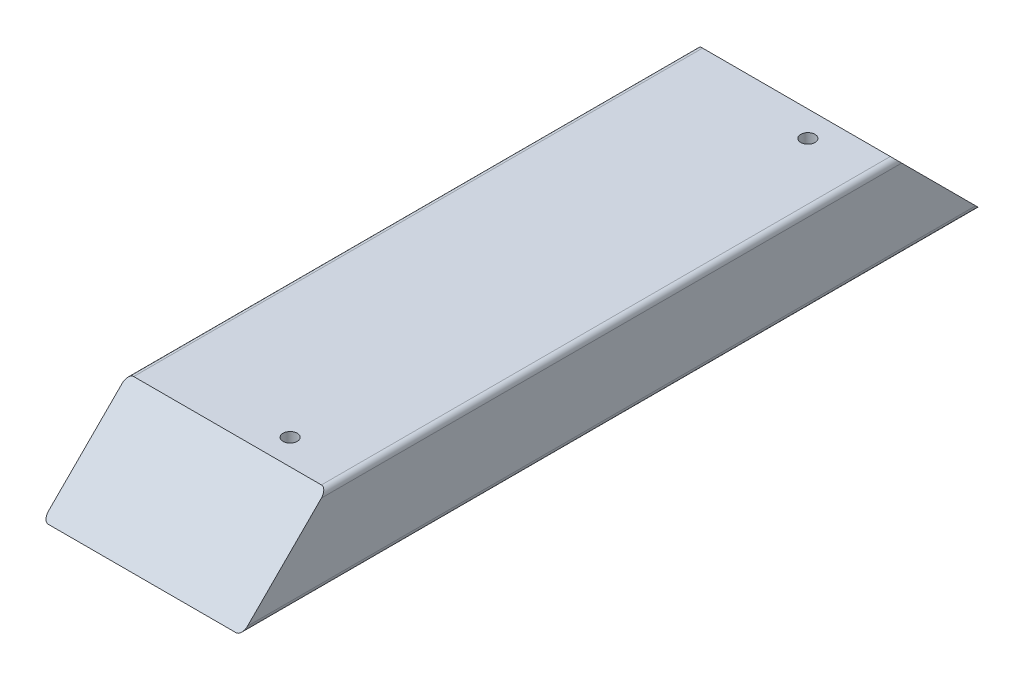
SolidWorks part; units mm, degrees
ref_plane "Front Plane" through (0, 0, 0) normal (0, 0, 1) x (1, 0, 0)
ref_plane "Top Plane" through (0, 0, 0) normal (0, 1, 0) x (1, 0, 0)
ref_plane "Right Plane" through (0, 0, 0) normal (1, 0, 0) x (0, 0, -1)
sketch "Sketch1" plane through (0, 0, 0) normal (0, 0, 1) x (1, 0, 0)
  line L1 (-44.45, 19.05) -> (44.45, 19.05)
  line L2 (-44.45, 19.05) -> (-44.45, -19.05)
  line L3 (-44.45, -19.05) -> (44.45, -19.05)
  line L4 (44.45, 19.05) -> (44.45, -19.05)
  line L5 (-44.45, 19.05) -> (44.45, -19.05) construction
  line L6 (-44.45, -19.05) -> (44.45, 19.05) construction
  point P0 (0, 0)
  dimension "D1" = 88.9
  dimension "D2" = 38.1
extrude "Boss-Extrude1" add sketch "Sketch1" along normal blind 330.2
fillet "Fillet1" radius 2.54 4 edges at (-44.45, -19.05, 165.1) (44.45, -19.05, 165.1) (44.45, 19.05, 165.1) (-44.45, 19.05, 165.1)
sketch "Sketch2" plane through (-44.45, 0, 0) normal (-1, 0, 0) x (0, 0, 1)
  line L0 (0, 19.05) -> (0, -19.05)
  line L1 (330.2, -19.05) -> (0, -19.05) construction
  line L2 (0, -16.51) -> (0, -19.05) construction
  line L3 (0, -19.05) -> (38.1, 19.05)
  line L4 (0, 19.05) -> (330.2, 19.05) construction
  line L5 (38.1, 19.05) -> (0, 19.05)
  dimension "D1" = 45
extrude "Cut-Extrude1" cut sketch "Sketch2" against normal blind 406.4
ref_plane "Plane1" through (0, 0, 165.1) normal (0, 0, 1) x (1, 0, 0)
mirror "Mirror1" about plane through (0, 0, 165.1) normal (0, 0, 1) of "Cut-Extrude1"
sketch "Sketch3" plane through (0, 19.05, 0) normal (0, 1, 0) x (1, 0, 0)
  line L0 (-41.91, 0) -> (41.91, 0) construction
  line L1 (41.91, -38.1) -> (-41.91, -38.1) construction
  circle A0 centre (16.51, -49.53) radius 3.175
  point P2 (0, 0)
  dimension "D2" = 6.35
  dimension "D1" = 16.51
  dimension "D3" = 11.43
extrude "Cut-Extrude2" cut sketch "Sketch3" against normal blind 12.7
mirror "Mirror2" about plane through (0, 0, 165.1) normal (0, 0, 1) of "Cut-Extrude2"
